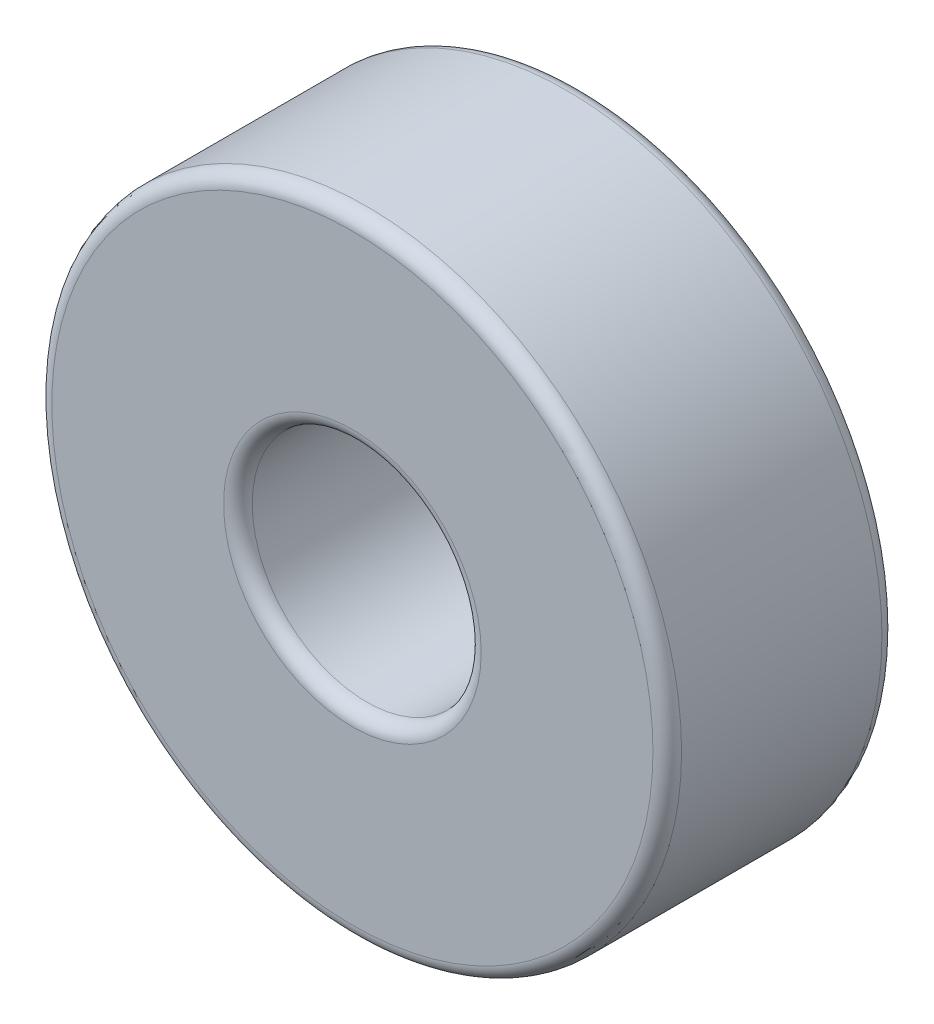
SolidWorks part; units mm, degrees
ref_plane "Plan de face" through (0, 0, 0) normal (0, 0, 1) x (1, 0, 0)
ref_plane "Plan de dessus" through (0, 0, 0) normal (0, 1, 0) x (1, 0, 0)
ref_plane "Plan de droite" through (0, 0, 0) normal (1, 0, 0) x (0, 0, -1)
sketch "Esquisse1" plane through (0, 0, 0) normal (0, 0, 1) x (1, 0, 0)
  circle A0 centre (0, 0) radius 11
  circle A1 centre (0, 0) radius 4
extrude "Extrusion1" add sketch "Esquisse1" along normal blind 8
fillet "Congé1" radius 0.5 4 edges at (4, 0, 0) (4, 0, 8) (11, 0, 0) (11, 0, 8)
